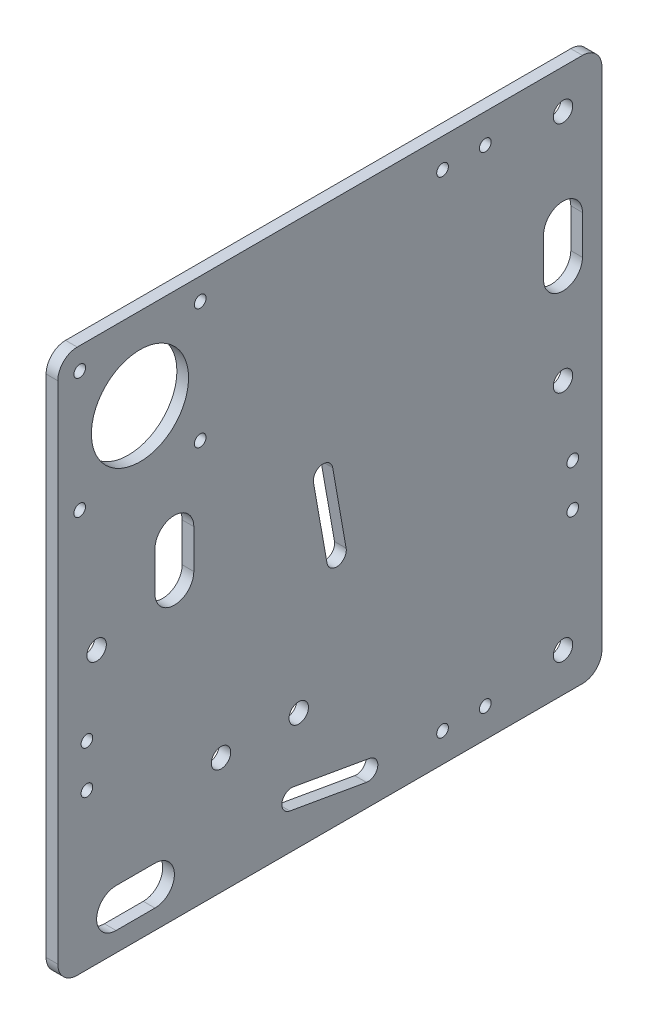
SolidWorks part; units mm, degrees
ref_plane "Front Plane" through (0, 0, 0) normal (0, 0, 1) x (1, 0, 0)
ref_plane "Top Plane" through (0, 0, 0) normal (0, 1, 0) x (1, 0, 0)
ref_plane "Right Plane" through (0, 0, 0) normal (1, 0, 0) x (0, 0, -1)
sketch "Sketch1" plane through (0, 0, 0) normal (1, 0, 0) x (0, 0, -1)
  line L0 (-70, 0) -> (70, 0)
  line L1 (70, 0) -> (70, 140)
  line L5 (-70, 140) -> (-70, 0)
  line L6 (70, 140) -> (-70, 140)
  point P2 (0, 0)
  dimension "D1" = 140
  dimension "D4" = 140
extrude "Base Plate" add sketch "Sketch1" along normal blind 3
fillet "Base Plate Corner Rounding" radius 5 4 edges at (1.5, 140, 70) (1.5, 140, -70) (1.5, 0, -70) (1.5, 0, 70)
sketch "Sketch2" plane through (3, 0, 0) normal (1, 0, 0) x (0, 0, -1)
  line L0 (70, 5) -> (70, 135) construction
  line L2 (-65, 0) -> (65, 0) construction
  line L3 (-70, 135) -> (-70, 5) construction
  line L4 (-9.8481, 11.7365) -> (9.8481, 8.2635) construction
  line L5 (-9.414, 14.1985) -> (10.2822, 10.7255)
  line L6 (65, 140) -> (-65, 140) construction
  line L7 (-10.2822, 9.2745) -> (9.414, 5.8015)
  line L8 (-1.7365, 79.8481) -> (1.7365, 60.1519) construction
  line L9 (0.7255, 80.2822) -> (4.1985, 60.586)
  line L10 (-4.1985, 79.414) -> (-0.7255, 59.7178)
  arc A0 (-9.414, 14.1985) -> (-10.2822, 9.2745) centre (-9.8481, 11.7365) ccw
  arc A1 (9.414, 5.8015) -> (10.2822, 10.7255) centre (9.8481, 8.2635) ccw
  circle A2 centre (60, 70) radius 2.5
  circle A3 centre (-60, 70) radius 2.5
  arc A4 (0.7255, 80.2822) -> (-4.1985, 79.414) centre (-1.7365, 79.8481) ccw
  arc A5 (-0.7255, 59.7178) -> (4.1985, 60.586) centre (1.7365, 60.1519) ccw
  circle A7 centre (60, 10) radius 2.5
  circle A8 centre (60, 130) radius 2.5
  point P9 (0, 10)
  point P20 (0, 70)
  dimension "D1" = 10
  dimension "D2" = 10
  dimension "D3" = 10
  dimension "D5" = 60
  dimension "D7" = 10
  dimension "D8" = 10
  dimension "D6" = 10
  dimension "D4" = 5
  dimension "D9" = 2.5
  dimension "D10" = 10
  dimension "D11" = 10
  dimension "D12" = 60
  dimension "D13" = 20
  dimension "D14" = 60
extrude "V Wheel Slots and Holes" cut sketch "Sketch2" against normal through all
sketch "Sketch4" plane through (3, 0, 0) normal (1, 0, 0) x (0, 0, -1)
  line L0 (-70, 135) -> (-70, 5) construction
  line L1 (65, 140) -> (-65, 140) construction
  circle A0 centre (-64.35, 134.35) radius 1.5
  dimension "D1" = 3
  dimension "D2" = 5.65
  dimension "D3" = 5.65
extrude "Motor Mount Holes" cut sketch "Sketch4" against normal through all
pattern_linear "Motor Mount Holes Pattern" count 2 spacing 31 along (0, 0, -1) count 2 spacing 31 along (0, -1, 0) of "Motor Mount Holes"
sketch "Sketch5" plane through (3, 0, 0) normal (1, 0, 0) x (0, 0, -1)
  line L0 (-64.35, 134.35) -> (-33.35, 103.35) construction
  circle A0 centre (-48.85, 118.85) radius 12.5
  point P2 (-48.85, 118.85)
  dimension "D1" = 25
extrude "Motor Hole" cut sketch "Sketch5" against normal through all
sketch "Sketch6" plane through (3, 0, 0) normal (1, 0, 0) x (0, 0, -1)
  circle A0 centre (-8, 30) radius 2.5
  circle A1 centre (-28, 30) radius 2.5
  circle A2 centre (60, 10) radius 2.5 construction
  dimension "D1" = 5
  dimension "D2" = 20
  dimension "D3" = 20
  dimension "D4" = 68
extrude "Threaded Rod Block Mounting Holes" cut sketch "Sketch6" against normal through all
sketch "Sketch7" plane through (3, 0, 0) normal (1, 0, 0) x (0, 0, -1)
  line L0 (-70, 135) -> (-70, 5) construction
  line L1 (70, 5) -> (70, 135) construction
  line L2 (-65, 0) -> (65, 0) construction
  line L3 (65, 140) -> (-65, 140) construction
  line L6 (70, 5) -> (70, 135) construction
  line L7 (-65, 0) -> (65, 0) construction
  circle A0 centre (-62.5, 51) radius 1.5
  circle A1 centre (-62.5, 40) radius 1.5
  circle A2 centre (62.5, 51) radius 1.5
  circle A3 centre (62.5, 40) radius 1.5
  circle A4 centre (40, 132.5) radius 1.5
  circle A5 centre (29, 132.5) radius 1.5
  circle A6 centre (40, 7.5) radius 1.5
  circle A7 centre (29, 7.5) radius 1.5
  dimension "D1" = 3
  dimension "D2" = 7.5
  dimension "D3" = 7.5
  dimension "D4" = 7.5
  dimension "D5" = 7.5
  dimension "D6" = 11
  dimension "D7" = 11
  dimension "D8" = 11
  dimension "D9" = 11
  dimension "D10" = 40
  dimension "D12" = 30
extrude "Endstop Mounting Holes" cut sketch "Sketch7" against normal through all
sketch "Sketch8" plane through (3, 0, 0) normal (1, 0, 0) x (0, 0, -1)
  line L0 (60, 105) -> (60, 95) construction
  line L1 (65, 105) -> (65, 95)
  line L2 (55, 105) -> (55, 95)
  line L3 (70, 5) -> (70, 135) construction
  line L7 (65, 140) -> (-65, 140) construction
  line L8 (-40, 85) -> (-40, 75) construction
  line L9 (-35, 85) -> (-35, 75)
  line L10 (-45, 85) -> (-45, 75)
  line L11 (-55, 10) -> (-45, 10) construction
  line L12 (-55, 15) -> (-45, 15)
  line L13 (-55, 5) -> (-45, 5)
  line L14 (-65, 0) -> (65, 0) construction
  line L15 (-70, 135) -> (-70, 5) construction
  arc A0 (65, 105) -> (55, 105) centre (60, 105) ccw
  arc A1 (55, 95) -> (65, 95) centre (60, 95) ccw
  circle A2 centre (60, 70) radius 2.5 construction
  arc A5 (-35, 85) -> (-45, 85) centre (-40, 85) ccw
  arc A6 (-45, 75) -> (-35, 75) centre (-40, 75) ccw
  arc A7 (-55, 15) -> (-55, 5) centre (-55, 10) ccw
  arc A8 (-45, 5) -> (-45, 15) centre (-45, 10) ccw
  point P2 (60, 100)
  point P22 (-40, 80)
  point P29 (-50, 10)
  dimension "D1" = 10
  dimension "D2" = 10
  dimension "D3" = 30
  dimension "D4" = 10
  dimension "D5" = 30
  dimension "D8" = 60
  dimension "D9" = 10
  dimension "D10" = 20
extrude "Wire Routing Slots" cut sketch "Sketch8" against normal through all
